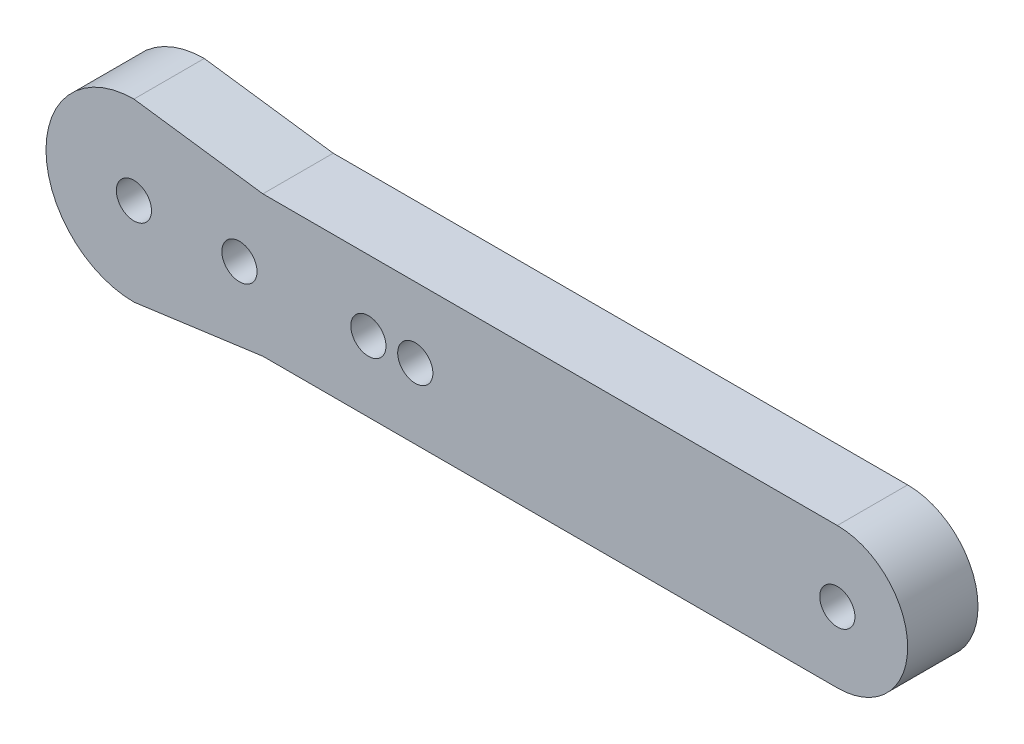
SolidWorks part; units mm, degrees
ref_plane "前视基准面" through (0, 0, 0) normal (0, 0, 1) x (1, 0, 0)
ref_plane "上视基准面" through (0, 0, 0) normal (0, 1, 0) x (1, 0, 0)
ref_plane "右视基准面" through (0, 0, 0) normal (1, 0, 0) x (0, 0, -1)
other "Configuration Table"
sketch "草图1" plane through (0, 0, 0) normal (0, 0, 1) x (1, 0, 0)
  line L0 (0, 0) -> (60, 0) construction
  line L1 (0, 6) -> (60, 6)
  line L2 (0, -6) -> (60, -6)
  arc A0 (0, 6) -> (0, -6) centre (0, 0) ccw
  arc A1 (60, -6) -> (60, 6) centre (60, 0) ccw
  point P3 (30, 0)
  dimension "D2" = 6
  dimension "D1" = 60
extrude "凸台-拉伸1" add sketch "草图1" along normal blind 6
sketch "草图2" plane through (0, 0, 6) normal (0, 0, 1) x (1, 0, 0)
  line L0 (0, 0) -> (60, 0) construction
  arc A0 (60, -6) -> (60, 6) centre (60, 0) ccw construction
  arc A1 (60, -6) -> (60, 6) centre (60, 0) ccw
  point P0 (0, 0)
  point P4 (60, 0)
  point P11 (9, 0)
  point P13 (20, 0)
  point P15 (24, 0)
  dimension "D1" = 9
  dimension "D2" = 20
  dimension "D3" = 24
hole_wizard "M3 螺纹孔1" positions "草图2" profile "草图3" tap size "M3" standard "GB" end condition through all
sketch "草图3" plane through (0, 0, 6) normal (1, 0, 0) x (0, -1, 0)
  line L0 (0, 0) -> (0, 6)
  line L1 (0, 6) -> (1.5, 6)
  line L2 (1.5, 6) -> (1.5, 0)
  line L5 (1.5, 0) -> (0, 0)
  line L11 (0, -6.35) -> (0, 107.95) construction
  dimension "通孔螺纹孔钻头直径" = 3
  dimension "通孔螺纹孔钻头深度" = 6
cosmetic thread "孔螺蚊线1" parameters "D2"=3
cosmetic thread "孔螺蚊线2" parameters "D2"=3
cosmetic thread "孔螺蚊线3" parameters "D2"=3
cosmetic thread "孔螺蚊线4" parameters "D2"=3
cosmetic thread "孔螺蚊线5" parameters "D2"=3
sketch "草图4" plane through (0, 0, 0) normal (0, 0, 1) x (1, 0, 0)
  line L0 (0, 7.5) -> (11, 6)
  line L1 (60, 6) -> (0, 6) construction
  line L2 (0, 0) -> (31.9006, 0) construction
  line L3 (11, 6) -> (0, 6)
  line L4 (11, -6) -> (0, -6)
  line L5 (0, -7.5) -> (11, -6)
  line L7 (0, 6) -> (0, -6) construction
  arc A0 (0, 7.5) -> (0, -7.5) centre (0, 0) ccw
  arc A2 (0, 6) -> (0, -6) centre (0, 0) ccw construction
  arc A3 (0, 6) -> (0, -6) centre (0, 0) ccw
  dimension "D1" = 15
  dimension "D2" = 11
extrude "凸台-拉伸3" add sketch "草图4" along normal up to surface (6 mm away) up to face at (1.5, 0, 6)
equation "\"SmallArm\"= 135mm"
equation "\"BigArm\"= 150mm"
equation "\"SmallArmBack\"= 60mm"
